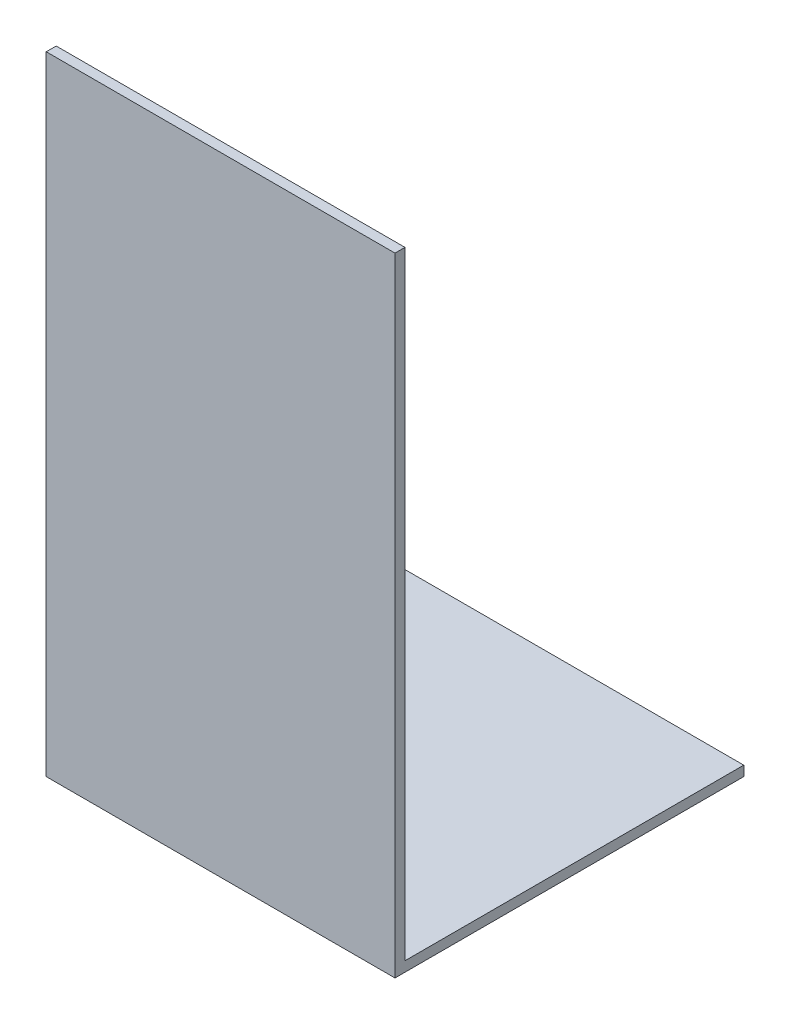
SolidWorks part; units mm, degrees
material "Plain Carbon Steel"
ref_plane "Front Plane" through (0, 0, 0) normal (0, 0, 1) x (1, 0, 0)
ref_plane "Top Plane" through (0, 0, 0) normal (0, 1, 0) x (1, 0, 0)
ref_plane "Right Plane" through (0, 0, 0) normal (1, 0, 0) x (0, 0, -1)
sketch "Sketch1" plane through (0, 0, 0) normal (0, 1, 0) x (1, 0, 0)
  line L1 (0, 0) -> (35, 0)
  line L2 (0, 0) -> (0, 35)
  line L3 (0, 35) -> (35, 35)
  line L4 (35, 0) -> (35, 35)
  dimension "D1" = 35
  dimension "D2" = 35
extrude "Boss-Extrude1" add sketch "Sketch1" along normal blind 1
sketch "Sketch2" plane through (0, 1, 0) normal (0, 1, 0) x (1, 0, 0)
  line L0 (0, 0) -> (0, 1)
  line L1 (0, 35) -> (0, 0) construction
  line L2 (0, 1) -> (35, 1)
  line L3 (35, 0) -> (35, 35) construction
  line L4 (35, 1) -> (35, 0)
  line L5 (35, 0) -> (0, 0)
  line L6 (0, 0) -> (0.2163, 0.0061)
  dimension "D1" = 1
extrude "Boss-Extrude2" add sketch "Sketch2" along normal blind 62
